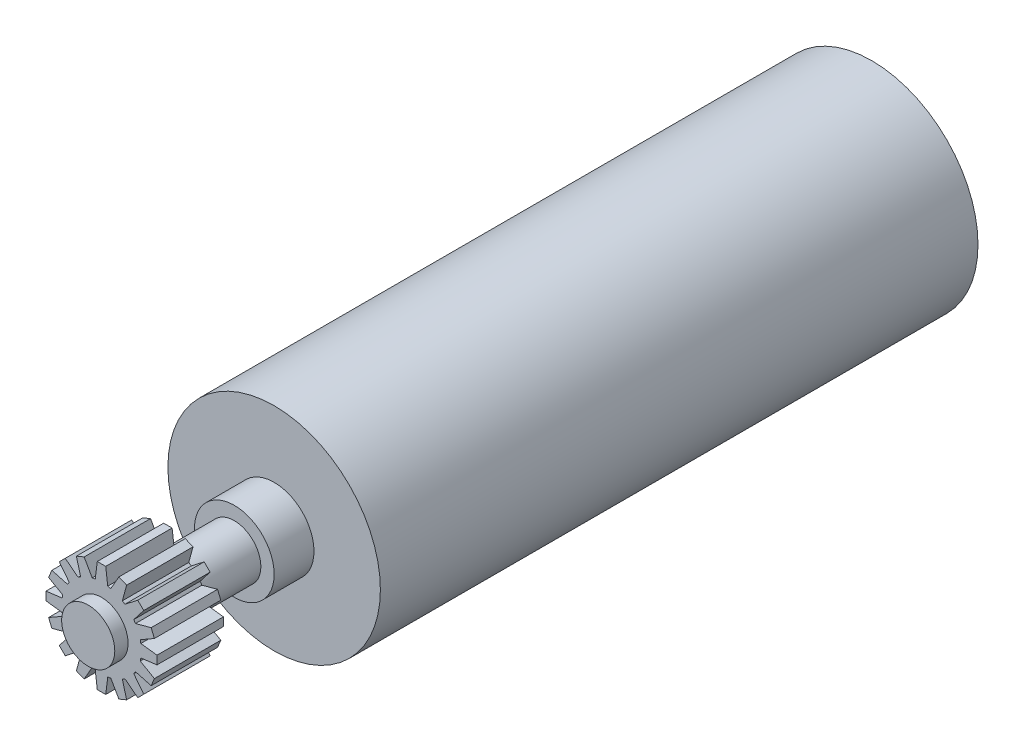
SolidWorks part; units mm, degrees
ref_plane "Plano frontal" through (0, 0, 0) normal (0, 0, 1) x (1, 0, 0)
ref_plane "Plano superior" through (0, 0, 0) normal (0, 1, 0) x (1, 0, 0)
ref_plane "Plano direito" through (0, 0, 0) normal (1, 0, 0) x (0, 0, -1)
sketch "Esboço1" plane through (0, 0, 0) normal (0, 0, 1) x (1, 0, 0)
  circle A0 centre (0, 0) radius 8
extrude "Ressalto-extrusão1" add sketch "Esboço1" along normal blind 45 contours A0
sketch "Esboço2" plane through (0, 0, 45) normal (0, 0, 1) x (1, 0, 0)
  circle A0 centre (0, 0) radius 3
extrude "Ressalto-extrusão2" add sketch "Esboço2" along normal blind 3 contours A0
sketch "Esboço3" plane through (0, 0, 48) normal (0, 0, 1) x (1, 0, 0)
  circle A0 centre (0, 0) radius 2
extrude "Ressalto-extrusão3" add sketch "Esboço3" along normal blind 5 contours A0
sketch "Esboço4" plane through (0, 0, 53) normal (0, 0, 1) x (1, 0, 0)
  line L0 (-12.6382, 0) -> (13.592, 0) construction
  circle A0 centre (0, 0) radius 3
extrude "Ressalto-extrusão4" add sketch "Esboço4" along normal blind 5 contours A0
sketch "Esboço5" plane through (0, 0, 58) normal (0, 0, 1) x (1, 0, 0)
  circle A0 centre (0, 0) radius 2
extrude "Ressalto-extrusão5" add sketch "Esboço5" along normal blind 1
sketch "Esboço6" plane through (0, 0, 58) normal (0, 0, 1) x (1, 0, 0)
  line L0 (0, 0) -> (0, 6.1157) construction
  line L1 (-0.5, 2.7357) -> (-0.3173, 4.179)
  line L2 (-0.3173, 4.179) -> (0.3173, 4.179)
  line L3 (0, 4.179) -> (0, 2.7357)
  line L4 (0.5, 2.7357) -> (-0.5, 2.7357)
  line L5 (0.5, 2.7357) -> (0.3173, 4.179)
extrude "Ressalto-extrusão6" add sketch "Esboço6" against normal blind 5 contours L1 L2 L5 L4
pattern_circular "PadrãoCircular1" count 16 over 360 about axis through (0, 0, 0) along (0, 0, 1) of "Ressalto-extrusão6"
